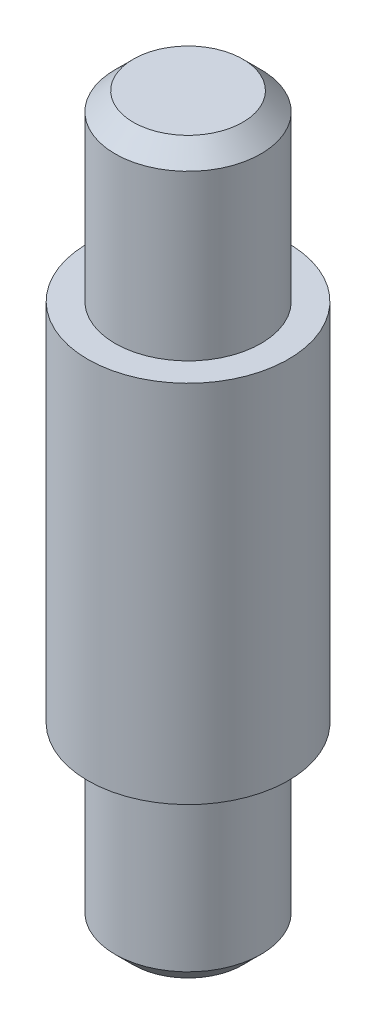
SolidWorks part; units mm, degrees
ref_plane "Alzado" through (0, 0, 0) normal (0, 0, 1) x (1, 0, 0)
ref_plane "Planta" through (0, 0, 0) normal (0, 1, 0) x (1, 0, 0)
ref_plane "Vista lateral" through (0, 0, 0) normal (1, 0, 0) x (0, 0, -1)
sketch "Croquis1" plane through (0, 0, 0) normal (0, 1, 0) x (1, 0, 0)
  circle A0 centre (0, 0) radius 8
extrude "Saliente-Extruir1" add sketch "Croquis1" along normal blind 80
ref_plane "Plano1" through (0, 40, 0) normal (0, 1, 0) x (1, 0, 0)
sketch "Croquis2" plane through (0, 40, 0) normal (0, 1, 0) x (1, 0, 0)
  circle A0 centre (0, 0) radius 11
  circle A1 centre (0, 0) radius 8 construction
extrude "Saliente-Extruir2" add sketch "Croquis2" along normal mid plane 40
chamfer "Chaflán1" distance 2 angle 45 1 edges at (0, 80, 8)
chamfer "Chaflán2" distance 2 angle 45 1 edges at (0, 0, 8)
